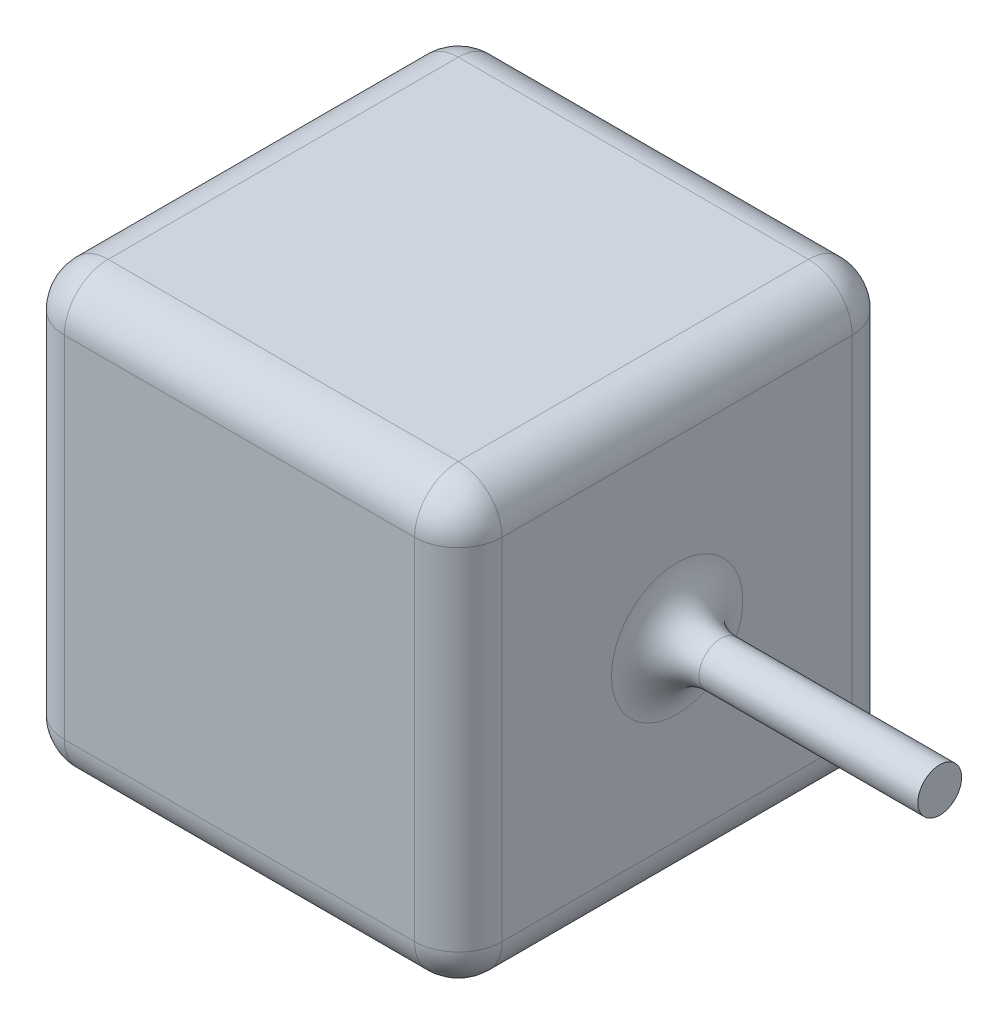
SolidWorks part; units mm, degrees
ref_plane "Front Plane" through (0, 0, 0) normal (0, 0, 1) x (1, 0, 0)
ref_plane "Top Plane" through (0, 0, 0) normal (0, 1, 0) x (1, 0, 0)
ref_plane "Right Plane" through (0, 0, 0) normal (1, 0, 0) x (0, 0, -1)
sketch "Sketch2" plane through (0, 0, 0) normal (0, 1, 0) x (1, 0, 0)
  line L1 (0, 0) -> (100, 0)
  line L2 (0, 0) -> (0, 100)
  line L3 (0, 100) -> (100, 100)
  line L4 (100, 0) -> (100, 100)
  dimension "D1" = 100
  dimension "D2" = 100
extrude "Boss-Extrude1" add sketch "Sketch2" along normal blind 100
sketch "Sketch3" plane through (100, 0, 0) normal (1, 0, 0) x (0, 0, -1)
  line L0 (0, 100) -> (0, 0) construction
  circle A0 centre (50, 50) radius 5
  dimension "D3" = 10
  dimension "D1" = 50
  dimension "D2" = 50
extrude "Boss-Extrude2" add sketch "Sketch3" along normal blind 60
fillet "Fillet5" radius 10 13 edges at (0, 50, -100) (50, 0, -100) (0, 0, -50) (100, 50, -100) (100, 0, -50) (100, 50, -45) (0, 50, 0) (100, 50, 0) (50, 0, 0) (50, 100, -100) (100, 100, -50) (50, 100, 0) (0, 100, -50)
